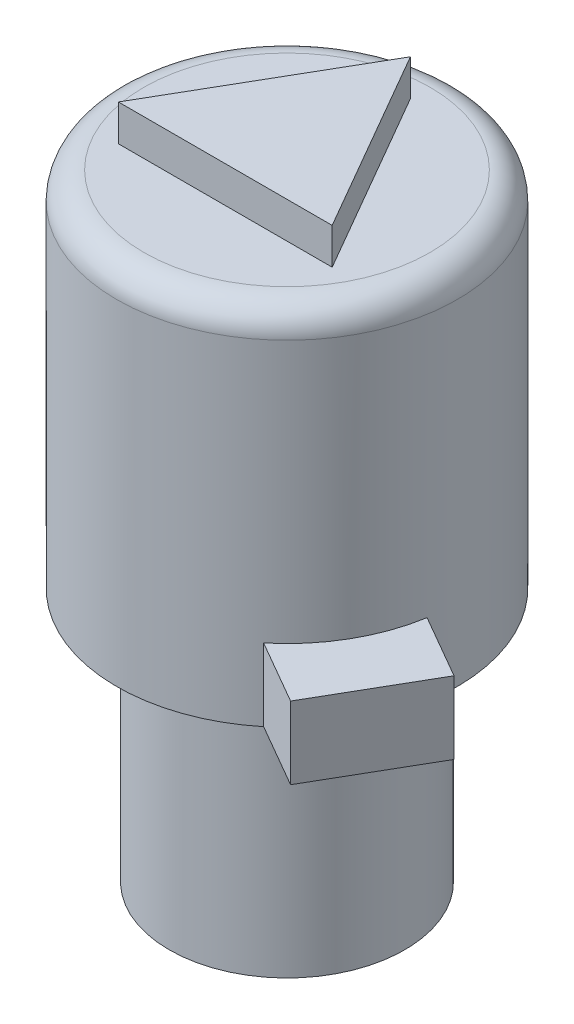
SolidWorks part; units mm, degrees
ref_plane "Front Plane" through (0, 0, 0) normal (0, 0, 1) x (1, 0, 0)
ref_plane "Top Plane" through (0, 0, 0) normal (0, 1, 0) x (1, 0, 0)
ref_plane "Right Plane" through (0, 0, 0) normal (1, 0, 0) x (0, 0, -1)
sketch "Sketch1" plane through (0, 0, 0) normal (0, 1, 0) x (1, 0, 0)
  circle A0 centre (0, 0) radius 3.25
  dimension "D1" = 6.5
extrude "Boss-Extrude1" add sketch "Sketch1" along normal blind 7.018 contours A0
sketch "Sketch2" plane through (0, 0, 0) normal (0, -1, 0) x (1, 0, 0)
  circle A1 centre (0, 0) radius 1.75
  dimension "D1" = 3.5
extrude "Cut-Extrude1" [suppressed] cut sketch "Sketch2" against normal blind 2.5
sketch "Sketch6" plane through (0, 7.018, 0) normal (0, 1, 0) x (1, 0, 0)
  circle A0 centre (0, 0) radius 4.7
  dimension "D1" = 9.4
extrude "Boss-Extrude2" add sketch "Sketch6" along normal blind 10 contours A0
sketch "Sketch7" plane through (0, 17.018, 0) normal (0, 1, 0) x (1, 0, 0)
  line L1 (2.95, -1.7032) -> (0, 3.4064)
  line L2 (0, 3.4064) -> (-2.95, -1.7032)
  line L3 (-2.95, -1.7032) -> (2.95, -1.7032)
  circle A0 centre (0, 0) radius 1.7032 construction
  dimension "D1" = 5.9
  dimension "D2" = 5.9
extrude "Boss-Extrude5" add sketch "Sketch7" along normal blind 1
fillet "Fillet1" radius 0.75 1 edges at (0, 17.018, 4.7)
sketch "Sketch8" plane through (0, 7.018, 0) normal (0, -1, 0) x (1, 0, 0)
  line L0 (-4.0703, -2.35) -> (4.0703, 2.35) construction
  line L1 (-4.7, 0) -> (4.7, 0) construction
  line L2 (-4.4821, -1.4146) -> (-6.2418, -2.4306)
  line L3 (-6.2418, -2.4306) -> (-5.2258, -4.1903)
  line L4 (-5.2258, -4.1903) -> (-3.4661, -3.1743)
  line L5 (2.9854, 3.63) -> (4.7452, 4.646)
  line L6 (4.7452, 4.646) -> (6.3962, 1.7864)
  line L7 (6.3962, 1.7864) -> (4.6364, 0.7704)
  circle A0 centre (0, 0) radius 4.7 construction
  arc A4 (-4.4821, -1.4146) -> (-3.4661, -3.1743) centre (0, 0) ccw
  arc A5 (4.6364, 0.7704) -> (2.9854, 3.63) centre (0, 0) ccw
  dimension "D1" = 30
  dimension "D2" = 1.016
  dimension "D3" = 1.016
  dimension "D4" = 2.032
  dimension "D5" = 2.032
  dimension "D6" = 1.651
  dimension "D7" = 1.651
extrude "Boss-Extrude6" add sketch "Sketch8" against normal blind 2
